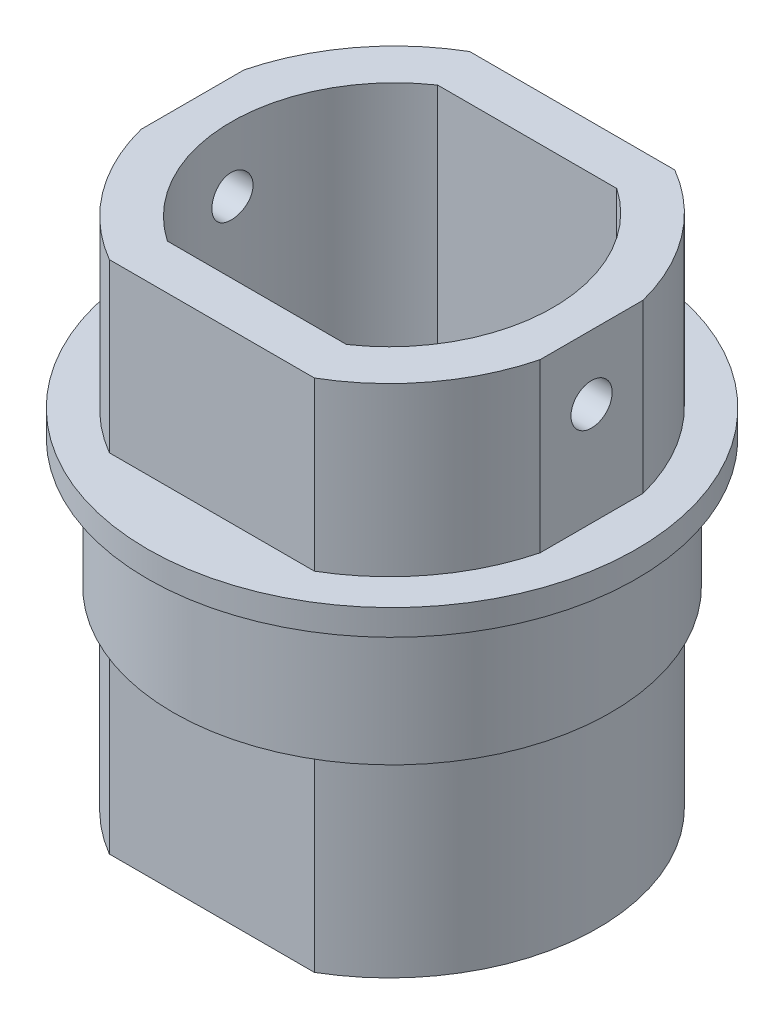
SolidWorks part; units mm, degrees
material "Nylon 101"
ref_plane "Front Plane" through (0, 0, 0) normal (0, 0, 1) x (1, 0, 0)
ref_plane "Top Plane" through (0, 0, 0) normal (0, 1, 0) x (1, 0, 0)
ref_plane "Right Plane" through (0, 0, 0) normal (1, 0, 0) x (0, 0, -1)
sketch "Sketch1" plane through (0, 0, 0) normal (0, 1, 0) x (1, 0, 0)
  line L0 (-2.5, 0) -> (2.5, 0) construction
  line L6 (-5.9, 6) -> (5, 6)
  line L7 (-5.9, 6) -> (-5.9, -6)
  line L8 (-5.9, -6) -> (5, -6)
  line L9 (5, 6) -> (5, -6)
  circle A0 centre (-2.5, 0) radius 1.2 construction
  circle A1 centre (2.5, 0) radius 1.2 construction
  point P0 (0, 0)
  point P9 (0, 0)
  point P11 (-5.9, 0)
  dimension "D1" = 2.4
  dimension "D2" = 5
  dimension "D3" = 10.9
  dimension "D4" = 12
  dimension "D5" = 3.4
sketch "Sketch5" plane through (0, 0, 0) normal (0, 1, 0) x (1, 0, 0)
  line L4 (-0.1077, 0) -> (0.1077, 0) construction
  line L5 (-3.4, -5) -> (3.4, -5)
  line L6 (-3.4, 5) -> (3.4, 5)
  line L8 (-3.9831, -7) -> (3.9831, -7)
  line L9 (-3.9831, 7) -> (3.9831, 7)
  arc A4 (3.4, 5) -> (3.4, -5) centre (-0.1077, 0) cw
  arc A5 (-3.4, 5) -> (-3.4, -5) centre (0.1077, 0) ccw
  arc A10 (3.9831, 7) -> (3.9831, -7) centre (-0.1077, 0) cw
  arc A11 (-3.9831, 7) -> (-3.9831, -7) centre (0.1077, 0) ccw
  point P1 (-6, 0)
  point P7 (6, 0)
  point P9 (0, 0)
  dimension "D1" = 6.8
  dimension "D2" = 12
  dimension "D3" = 10
  dimension "D4" = 10
  dimension "D6" = 2
extrude "Boss-Extrude3" add sketch "Sketch5" along normal blind 20
sketch "Sketch7" plane through (0, 0, 0) normal (0, 1, 0) x (1, 0, 0)
  line L3 (3.9831, 7) -> (-3.9831, 7)
  line L6 (-3.9831, -7) -> (3.9831, -7)
  line L7 (3.9831, 7) -> (-3.9831, 7)
  line L10 (-3.9831, -7) -> (3.9831, -7)
  arc A3 (-3.9831, 7) -> (-3.9831, -7) centre (0.1077, 0) ccw
  arc A7 (3.9831, -7) -> (3.9831, 7) centre (-0.1077, 0) ccw
  arc A9 (-3.9831, 7) -> (-3.9831, -7) centre (0.1077, 0) ccw
  arc A10 (3.9831, -7) -> (3.9831, 7) centre (-0.1077, 0) ccw
  dimension "D1" = 0
extrude "Boss-Extrude5" add sketch "Sketch7" along normal blind 1
sketch "Sketch16" plane through (0, 1, 0) normal (0, 1, 0) x (1, 0, 0)
  line L0 (3.4314, 5.1) -> (-3.4314, 5.1)
  line L1 (-3.4314, -5.1) -> (3.4314, -5.1)
  line L2 (3.4, 5) -> (-3.4, 5)
  line L3 (-3.4, -5) -> (3.4, -5)
  line L6 (3.4, 5) -> (-3.4, 5) construction
  line L7 (-3.4, -5) -> (3.4, -5) construction
  arc A0 (-3.4314, 5.1) -> (-3.4314, -5.1) centre (0.1077, 0) ccw
  arc A1 (3.4314, -5.1) -> (3.4314, 5.1) centre (-0.1077, 0) ccw
  arc A2 (-3.4, 5) -> (-3.4, -5) centre (0.1077, 0) ccw
  arc A3 (3.4, -5) -> (3.4, 5) centre (-0.1077, 0) ccw
  arc A6 (-3.4, 5) -> (-3.4, -5) centre (0.1077, 0) ccw construction
  arc A7 (3.4, -5) -> (3.4, 5) centre (-0.1077, 0) ccw construction
  dimension "D1" = 0
  dimension "D2" = 0.1
sketch "Sketch18" plane through (0, 0, -5) normal (0, 0, 1) x (1, 0, 0)
  line L1 (3.4, 1) -> (-3.4, 1)
  line L2 (3.4, 1) -> (3.4, 6)
  line L3 (3.4, 6) -> (-3.4, 6)
  line L4 (-3.4, 1) -> (-3.4, 6)
  dimension "D2" = 5
extrude "Cut-Extrude3" cut sketch "Sketch18" against normal through all
sketch "Sketch24" plane through (0, 0, 0) normal (0, 0, 1) x (1, 0, 0)
  line L0 (0, 0) -> (0, 50000) construction
ref_plane "Plane4" through (0, 10, 0) normal (0, 1, 0) x (1, 0, 0)
sketch "Sketch25" plane through (0, 10, 0) normal (0, 1, 0) x (1, 0, 0)
  line L2 (3.9831, 7) -> (-3.9831, 7)
  line L3 (-3.9831, -7) -> (3.9831, -7)
  line L4 (3.9831, 7) -> (-3.9831, 7)
  line L5 (-3.9831, -7) -> (3.9831, -7)
  circle A0 centre (0, 0) radius 8.5
  arc A3 (-3.9831, 7) -> (-3.9831, -7) centre (0.1077, 0) ccw
  arc A4 (3.9831, -7) -> (3.9831, 7) centre (-0.1077, 0) ccw
  arc A5 (-3.9831, 7) -> (-3.9831, -7) centre (0.1077, 0) ccw
  arc A6 (3.9831, -7) -> (3.9831, 7) centre (-0.1077, 0) ccw
  dimension "D2" = 17
  dimension "D1" = 0
extrude "Boss-Extrude6" add sketch "Sketch25" along normal mid plane 5
sketch "Sketch26" plane through (0, 12.5, 0) normal (0, 1, 0) x (1, 0, 0)
  line L2 (3.9831, 7) -> (-3.9831, 7)
  line L3 (-3.9831, -7) -> (3.9831, -7)
  line L4 (3.9831, 7) -> (-3.9831, 7)
  line L5 (-3.9831, -7) -> (3.9831, -7)
  arc A2 (-3.9831, 7) -> (-3.9831, -7) centre (0.1077, 0) ccw
  arc A3 (3.9831, -7) -> (3.9831, 7) centre (-0.1077, 0) ccw
  arc A4 (-3.9831, 7) -> (-3.9831, -7) centre (0.1077, 0) ccw
  arc A5 (3.9831, -7) -> (3.9831, 7) centre (-0.1077, 0) ccw
  circle A6 centre (0, 0) radius 9.5
  circle A7 centre (0, 0) radius 9.5
  dimension "D1" = 0
  dimension "D2" = 1
extrude "Boss-Extrude7" add sketch "Sketch26" along normal blind 1
sketch "Sketch32" plane through (0, 0, 0) normal (0, -1, 0) x (1, 0, 0)
  line L0 (-1.7321, 1) -> (1.7321, 1)
  arc A0 (-1.7321, 1) -> (1.7321, 1) centre (0, 0) ccw
  dimension "D1" = 2
  dimension "D2" = 1
extrude "Boss-Extrude11" add sketch "Sketch32" along normal blind 4
sketch "Sketch34" plane through (0, -4, 0) normal (0, -1, 0) x (1, 0, 0)
  line L0 (-1.118, 1) -> (1.118, 1)
  arc A0 (-1.118, 1) -> (1.118, 1) centre (0, 0) ccw
  point P1 (0, -1.5)
  dimension "D1" = 1.5
  dimension "D2" = 2.5
extrude "Cut-Extrude7" cut sketch "Sketch34" against normal blind 4
sketch "Sketch35" plane through (0, 0, 0) normal (0, -1, 0) x (1, 0, 0)
  line L0 (-1.118, 1) -> (1.118, 1)
  circle A0 centre (0, 0) radius 3.5
  arc A1 (-1.118, 1) -> (1.118, 1) centre (0, 0) ccw
  arc A2 (-1.118, 1) -> (1.118, 1) centre (0, 0) ccw construction
  dimension "D1" = 7
  dimension "D2" = 1
extrude "Boss-Extrude12" add sketch "Sketch35" along normal blind 2
sketch "Sketch36" plane through (0, 0, 0) normal (1, 0, 0) x (0, 0, -1)
  line L0 (0, -200000) -> (0, 250000) construction
  line L1 (7, 20) -> (-7, 20) construction
  circle A0 centre (0, 17.5) radius 0.8
  dimension "D1" = 1.6
  dimension "D2" = 2.5
extrude "Cut-Extrude8" cut sketch "Sketch36" against normal through all both and the other way through all
sketch "Sketch37" plane through (0, 20, 0) normal (0, 1, 0) x (1, 0, 0)
  line L0 (7.75, -1.9978) -> (7.75, 1.9978)
  line L1 (0, -3.5879) -> (0, 3.5879) construction
  line L2 (-7.75, -1.9978) -> (-7.75, 1.9978)
  arc A0 (3.4, -5) -> (3.4, 5) centre (-0.1077, 0) ccw construction
  arc A1 (3.9831, -7) -> (3.9831, 7) centre (-0.1077, 0) ccw construction
  arc A2 (7.75, -1.9978) -> (7.75, 1.9978) centre (-0.1077, 0) ccw
  arc A3 (-7.75, -1.9978) -> (-7.75, 1.9978) centre (0.1077, 0) cw
  point P2 (6, 0)
  point P15 (0, 0)
  point P17 (-6, 0)
  dimension "D1" = 1.75
extrude "Cut-Extrude9" cut sketch "Sketch37" against normal up to surface (6.5 mm away) up to face at (0, 13.5, 9.5)
sketch "Sketch38" plane through (0, 0, 0) normal (0, -1, 0) x (1, 0, 0)
  line L3 (1.1619, 1.1) -> (-1.1619, 1.1)
  line L4 (1.1619, 1.1) -> (-1.1619, 1.1)
  arc A3 (-1.1619, 1.1) -> (1.1619, 1.1) centre (0, 0) ccw
  arc A4 (-1.1619, 1.1) -> (1.1619, 1.1) centre (0, 0) ccw
  dimension "D1" = 0.1
extrude "Cut-Extrude10" cut sketch "Sketch38" along normal through all
sketch "Sketch39" plane through (0, 20, 0) normal (0, 1, 0) x (1, 0, 0)
  line L20 (-3.4, 5) -> (3.4, 5) construction
  line L21 (-3.4, -5) -> (3.4, -5) construction
  line L22 (3.4781, 5.25) -> (-3.4781, 5.25)
  line L23 (-3.4781, -5.25) -> (3.4781, -5.25)
  line L24 (3.4781, 5.25) -> (-3.4781, 5.25)
  line L25 (-3.4781, -5.25) -> (3.4781, -5.25)
  line L26 (-3.4, 5) -> (3.4, 5)
  line L27 (-3.4, -5) -> (3.4, -5)
  arc A13 (-3.4, 5) -> (-3.4, -5) centre (0.1077, 0) ccw construction
  arc A14 (3.4, -5) -> (3.4, 5) centre (-0.1077, 0) ccw construction
  arc A15 (3.4781, -5.25) -> (3.4781, 5.25) centre (-0.1077, 0) ccw
  arc A20 (-3.4781, 5.25) -> (-3.4781, -5.25) centre (0.1077, 0) ccw
  arc A21 (3.4781, -5.25) -> (3.4781, 5.25) centre (-0.1077, 0) ccw
  arc A22 (-3.4781, 5.25) -> (-3.4781, -5.25) centre (0.1077, 0) ccw
  arc A23 (-3.4, 5) -> (-3.4, -5) centre (0.1077, 0) ccw
  arc A24 (3.4, -5) -> (3.4, 5) centre (-0.1077, 0) ccw
  dimension "D1" = 0.25
extrude "Cut-Extrude11" cut sketch "Sketch39" against normal up to surface (19 mm away) up to face at (0, 1, -2.3333)
